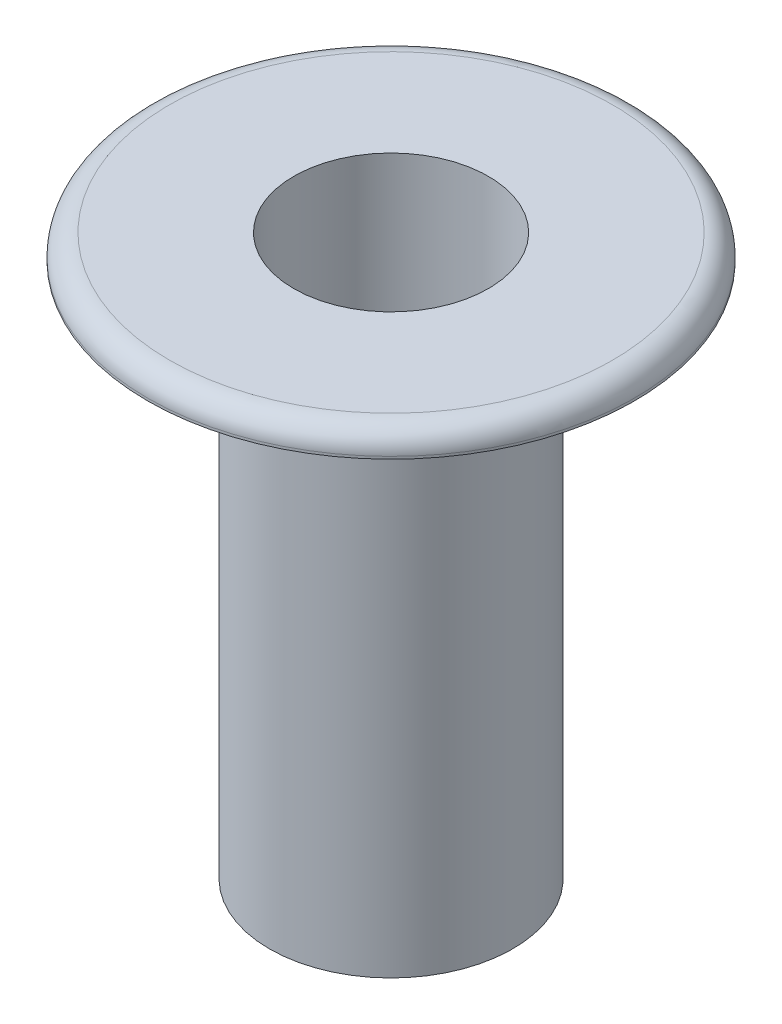
SolidWorks part; units mm, degrees
ref_plane "Front Plane" through (0, 0, 0) normal (0, 0, 1) x (1, 0, 0)
ref_plane "Top Plane" through (0, 0, 0) normal (0, 1, 0) x (1, 0, 0)
ref_plane "Right Plane" through (0, 0, 0) normal (1, 0, 0) x (0, 0, -1)
sketch "Sketch1" plane through (0, 0, 0) normal (0, 1, 0) x (1, 0, 0)
  circle A0 centre (0, 0) radius 1.25
  circle A1 centre (0, 0) radius 1
extrude "Boss-Extrude1" add sketch "Sketch1" along normal blind 5.5
sketch "Sketch2" plane through (0, 5.5, 0) normal (0, 1, 0) x (1, 0, 0)
  circle A0 centre (0, 0) radius 1
  circle A1 centre (0, 0) radius 2.5
extrude "Boss-Extrude2" add sketch "Sketch2" along normal blind 0.25
fillet "Fillet1" radius 0.225 1 edges at (0, 5.75, 2.5)
